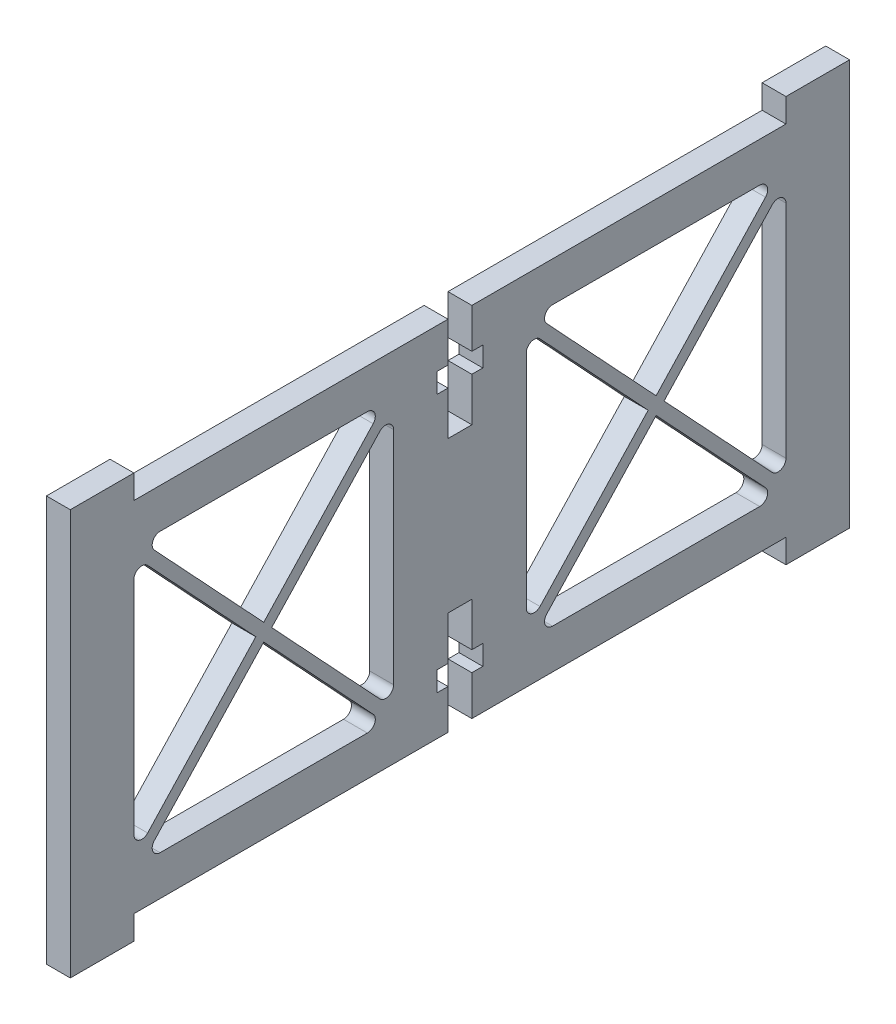
SolidWorks part; units mm, degrees
ref_plane "Plano frontal" through (0, 0, 0) normal (0, 0, 1) x (1, 0, 0)
ref_plane "Plano superior" through (0, 0, 0) normal (0, 1, 0) x (1, 0, 0)
ref_plane "Plano direito" through (0, 0, 0) normal (1, 0, 0) x (0, 0, -1)
sketch "Esboço1" plane through (0, 0, 0) normal (1, 0, 0) x (0, 0, -1)
  line L0 (49, 1.5) -> (41, 1.5)
  line L1 (49, -1.5) -> (49, 1.5)
  line L3 (41, 1.5) -> (41, -1.5)
  line L4 (-41, 1.5) -> (-49, 1.5)
  line L5 (-41, -1.5) -> (-41, 1.5)
  line L7 (-49, 1.5) -> (-49, -1.5)
  line L8 (-49, -1.5) -> (-49, -46.5)
  line L9 (-41, -10.1092) -> (-41, -37.8908)
  line L10 (2.875, -9) -> (2.875, -6.5)
  line L11 (-1.5, -1.5) -> (-1.5, -6.5)
  line L12 (-1.5, -14.5) -> (1.5, -14.5)
  line L13 (1.5, -14.5) -> (1.5, -9)
  line L14 (-2.875, -9) -> (-1.5, -9)
  line L15 (2.875, -6.5) -> (1.5, -6.5)
  line L16 (-2.875, -6.5) -> (-2.875, -9)
  line L17 (-1.5, -6.5) -> (-2.875, -6.5)
  line L18 (-1.5, -9) -> (-1.5, -14.5)
  line L19 (1.5, -9) -> (2.875, -9)
  line L20 (1.5, -6.5) -> (1.5, -1.5)
  line L21 (-41, -1.5) -> (-1.5, -1.5)
  line L22 (1.5, -1.5) -> (33.4859, -1.5)
  line L23 (33.4859, -1.5) -> (41, -1.5)
  line L24 (49, -1.5) -> (49, -24)
  line L25 (33.4859, -46.5) -> (41, -46.5)
  line L26 (1.5, -46.5) -> (33.4859, -46.5)
  line L27 (-41, -46.5) -> (-1.5, -46.5)
  line L28 (1.5, -41.5) -> (1.5, -46.5)
  line L29 (1.5, -39) -> (2.875, -39)
  line L30 (-1.5, -39) -> (-1.5, -33.5)
  line L31 (-1.5, -41.5) -> (-2.875, -41.5)
  line L32 (-2.875, -41.5) -> (-2.875, -39)
  line L33 (2.875, -41.5) -> (1.5, -41.5)
  line L34 (-2.875, -39) -> (-1.5, -39)
  line L35 (1.5, -33.5) -> (1.5, -39)
  line L36 (-1.5, -33.5) -> (1.5, -33.5)
  line L37 (-1.5, -46.5) -> (-1.5, -41.5)
  line L38 (2.875, -39) -> (2.875, -41.5)
  line L39 (-49, -49.5) -> (-49, -46.5)
  line L40 (-41, -46.5) -> (-41, -49.5)
  line L41 (-41, -49.5) -> (-49, -49.5)
  line L42 (41, -49.5) -> (41, -46.5)
  line L43 (49, -46.5) -> (49, -49.5)
  line L44 (49, -49.5) -> (41, -49.5)
  line L45 (49, -46.5) -> (49, -24)
  line L46 (-37.6992, -41.5) -> (-11.6421, -41.5)
  line L47 (-8.3413, -37.8908) -> (-8.3413, -10.1092)
  line L48 (-11.6421, -6.5) -> (-37.6992, -6.5)
  line L49 (-24.6707, -25.0717) -> (-38.4303, -39.8178)
  line L50 (-25.6707, -24) -> (-39.2689, -38.5731)
  line L52 (-24.6707, -22.9283) -> (-38.4303, -8.1822)
  line L53 (-23.6707, -24) -> (-10.0724, -38.5731)
  line L54 (-24.6707, -25.0717) -> (-10.911, -39.8178)
  line L55 (-25.6707, -24) -> (-39.2689, -9.4269)
  line L56 (-10.0724, -9.4269) -> (-23.6707, -24)
  line L57 (-10.911, -8.1822) -> (-24.6707, -22.9283)
  line L58 (10.911, -8.1822) -> (24.6707, -22.9283)
  line L59 (10.0724, -9.4269) -> (23.6707, -24)
  line L60 (25.6707, -24) -> (39.2689, -9.4269)
  line L61 (24.6707, -25.0717) -> (10.911, -39.8178)
  line L62 (23.6707, -24) -> (10.0724, -38.5731)
  line L63 (24.6707, -22.9283) -> (38.4303, -8.1822)
  line L64 (25.6707, -24) -> (39.2689, -38.5731)
  line L65 (24.6707, -25.0717) -> (38.4303, -39.8178)
  line L66 (11.6421, -6.5) -> (37.6992, -6.5)
  line L67 (8.3413, -37.8908) -> (8.3413, -10.1092)
  line L68 (37.6992, -41.5) -> (11.6421, -41.5)
  line L69 (41, -10.1092) -> (41, -37.8908)
  arc A0 (-38.4303, -8.1822) -> (-37.6992, -6.5) centre (-37.6992, -7.5) cw
  arc A1 (-39.2689, -9.4269) -> (-41, -10.1092) centre (-40, -10.1092) ccw
  arc A2 (-10.911, -8.1822) -> (-11.6421, -6.5) centre (-11.6421, -7.5) ccw
  arc A3 (-8.3413, -10.1092) -> (-10.0724, -9.4269) centre (-9.3413, -10.1092) ccw
  arc A4 (-10.0724, -38.5731) -> (-8.3413, -37.8908) centre (-9.3413, -37.8908) ccw
  arc A5 (-10.911, -39.8178) -> (-11.6421, -41.5) centre (-11.6421, -40.5) cw
  arc A6 (-37.6992, -41.5) -> (-38.4303, -39.8178) centre (-37.6992, -40.5) cw
  arc A7 (-39.2689, -38.5731) -> (-41, -37.8908) centre (-40, -37.8908) cw
  arc A8 (39.2689, -38.5731) -> (41, -37.8908) centre (40, -37.8908) ccw
  arc A9 (37.6992, -41.5) -> (38.4303, -39.8178) centre (37.6992, -40.5) ccw
  arc A10 (10.911, -39.8178) -> (11.6421, -41.5) centre (11.6421, -40.5) ccw
  arc A11 (10.0724, -38.5731) -> (8.3413, -37.8908) centre (9.3413, -37.8908) cw
  arc A12 (8.3413, -10.1092) -> (10.0724, -9.4269) centre (9.3413, -10.1092) cw
  arc A13 (10.911, -8.1822) -> (11.6421, -6.5) centre (11.6421, -7.5) cw
  arc A14 (39.2689, -9.4269) -> (41, -10.1092) centre (40, -10.1092) cw
  arc A15 (38.4303, -8.1822) -> (37.6992, -6.5) centre (37.6992, -7.5) ccw
  dimension "D1" = 1
  dimension "D2" = 1
  dimension "D3" = 1
  dimension "D4" = 1
  dimension "D5" = 1
  dimension "D6" = 1
  dimension "D7" = 1
  dimension "D8" = 1
extrude "Ressalto-extrusão1" add sketch "Esboço1" along normal blind 3
